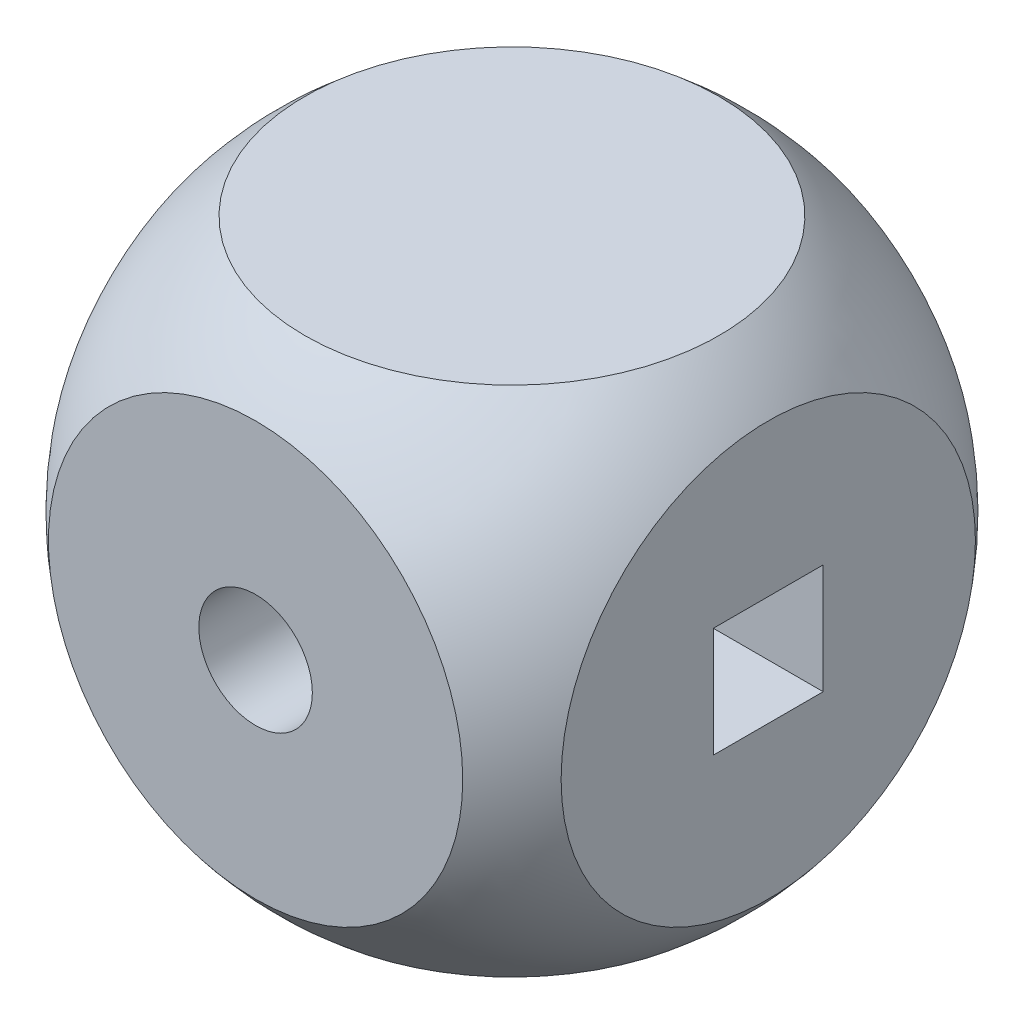
SolidWorks part; units mm, degrees
ref_plane "정면" through (0, 0, 0) normal (0, 0, 1) x (1, 0, 0)
ref_plane "윗면" through (0, 0, 0) normal (0, 1, 0) x (1, 0, 0)
ref_plane "우측면" through (0, 0, 0) normal (1, 0, 0) x (0, 0, -1)
sketch "스케치1" plane through (0, 0, 0) normal (0, 0, 1) x (1, 0, 0)
  line L0 (0, 0.8636) -> (0, -0.67) construction
  line L1 (0, 9) -> (0, -9)
  arc A0 (0, -9) -> (0, 9) centre (0, 0) ccw
  dimension "D1" = 18
revolve "회전42" add sketch "스케치1" angle 360 about L1
ref_plane "평면1" through (0, 0, 9) normal (0, 0, 1) x (1, 0, 0)
ref_plane "평면2" through (0, 9, 0) normal (0, 1, 0) x (1, 0, 0)
ref_plane "평면3" through (9, 0, 0) normal (1, 0, 0) x (0, 0, -1)
sketch "스케치6" plane through (0, 0, 9) normal (0, 0, 1) x (1, 0, 0)
  circle A0 centre (0, 0) radius 10
  dimension "D1" = 20
extrude "컷-돌출4" cut sketch "스케치6" against normal blind 2
mirror "대칭 복사4" about plane through (0, 0, 0) normal (0, 0, 1) of "컷-돌출4"
sketch "스케치7" plane through (0, 9, 0) normal (0, 1, 0) x (1, 0, 0)
  circle A0 centre (0, 0) radius 10
  dimension "D1" = 20
extrude "컷-돌출5" cut sketch "스케치7" against normal blind 2
mirror "대칭 복사5" about plane through (0, 0, 0) normal (0, 1, 0) of "컷-돌출5"
sketch "스케치8" plane through (9, 0, 0) normal (1, 0, 0) x (0, 0, -1)
  circle A0 centre (0, 0) radius 10
  dimension "D1" = 20
extrude "컷-돌출6" cut sketch "스케치8" against normal blind 2
mirror "대칭 복사6" about plane through (0, 0, 0) normal (1, 0, 0) of "컷-돌출6"
sketch "스케치9" plane through (0, 0, 7) normal (0, 0, 1) x (1, 0, 0)
  circle A0 centre (0, 0) radius 1.55
  dimension "D1" = 3.1
extrude "컷-돌출7" cut sketch "스케치9" against normal through all
sketch "스케치10" plane through (0, 7, 0) normal (0, 1, 0) x (1, 0, 0)
  circle A0 centre (0, 0) radius 1.55
  dimension "D1" = 3.1
sketch "스케치11" plane through (7, 0, 0) normal (1, 0, 0) x (0, 0, -1)
  line L1 (-1.5, 1.5) -> (1.5, 1.5)
  line L2 (-1.5, 1.5) -> (-1.5, -1.5)
  line L3 (-1.5, -1.5) -> (1.5, -1.5)
  line L4 (1.5, 1.5) -> (1.5, -1.5)
  line L5 (-1.5, 1.5) -> (1.5, -1.5) construction
  line L6 (-1.5, -1.5) -> (1.5, 1.5) construction
  dimension "D1" = 3
  dimension "D2" = 3
extrude "컷-돌출9" cut sketch "스케치11" against normal through all
sketch "스케치12" plane through (0, 0, 0) normal (0, 0, 1) x (1, 0, 0)
  circle A0 centre (0, 0) radius 9 construction
  circle A1 centre (0, 0) radius 9.25 construction
  dimension "D1" = 18
  dimension "D2" = 18.5
sketch "스케치13" plane through (0, 0, 7) normal (0, 0, 1) x (1, 0, 0)
  circle A0 centre (0, 0) radius 5.6569 construction
sketch "스케치14" plane through (0, 0, -7) normal (0, 0, -1) x (-1, 0, 0)
  circle A0 centre (0, 0) radius 5.6569 construction
